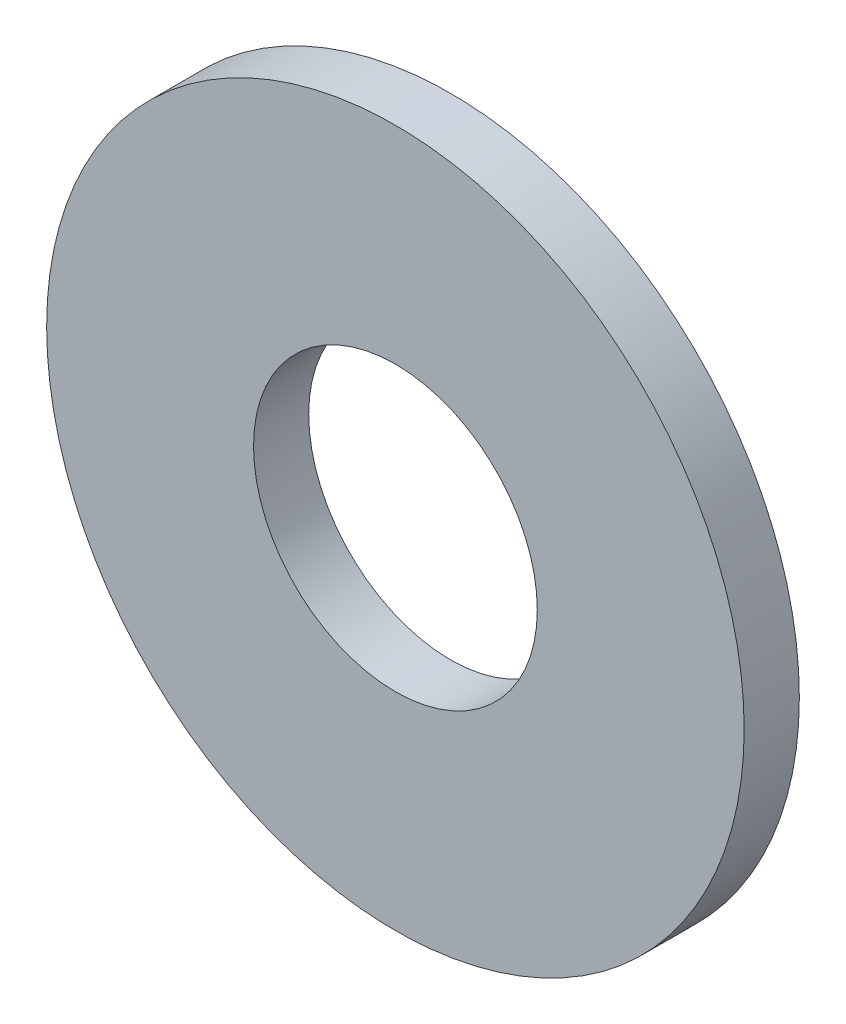
SolidWorks part; units mm, degrees
ref_plane "Спереди" through (0, 0, 0) normal (0, 0, 1) x (1, 0, 0)
ref_plane "Сверху" through (0, 0, 0) normal (0, 1, 0) x (1, 0, 0)
ref_plane "Справа" through (0, 0, 0) normal (1, 0, 0) x (0, 0, -1)
sketch "Sketch1" plane through (0, 0, 0) normal (0, 0, 1) x (1, 0, 0)
  circle A0 centre (0, 0) radius 8.85
  circle A1 centre (0, 0) radius 3.6
  dimension "D1" = 17.7
  dimension "D2" = 7.2
extrude "Boss-Extrude1" add sketch "Sketch1" along normal blind 1.4
